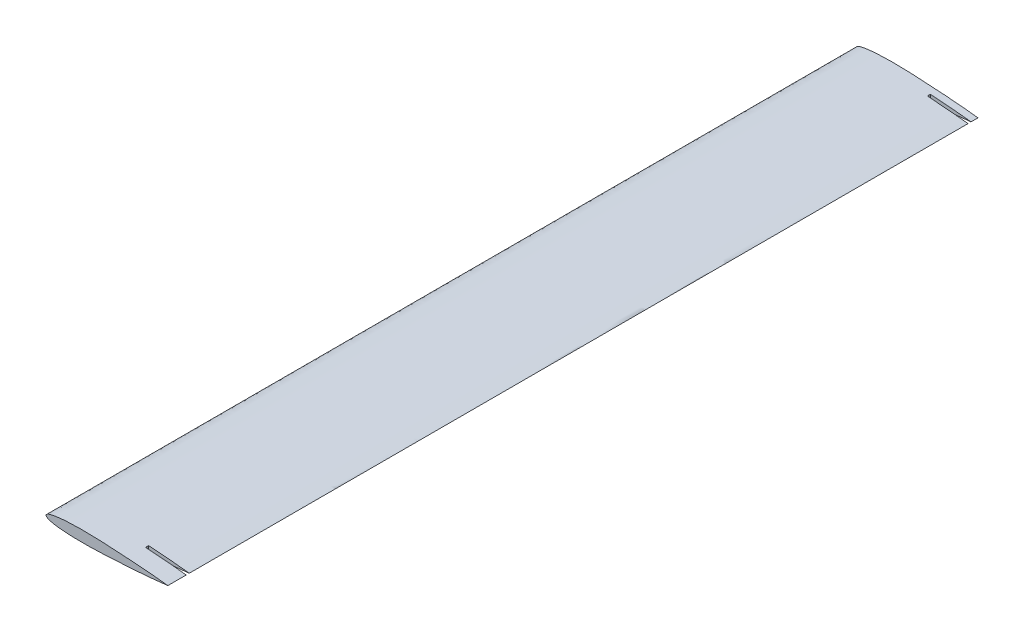
SolidWorks part; units mm, degrees
ref_plane "Front Plane" through (0, 0, 0) normal (0, 0, 1) x (1, 0, 0)
ref_plane "Top Plane" through (0, 0, 0) normal (0, 1, 0) x (1, 0, 0)
ref_plane "Right Plane" through (0, 0, 0) normal (1, 0, 0) x (0, 0, -1)
curve "Curve1"
  spline degree 3 poles (198.173, -0.1902, 0) (200.4592, 0, 0) (198.173, 0.1902, 0) (196.2993, 0.5074, 0) (191.7479, 0.9938, 0) (186.1558, 1.5974, 0) (178.8694, 2.3058, 0) (170.3147, 3.0876, 0) (160.5293, 3.9276, 0) (149.7178, 4.8013, 0) (138.0526, 5.6738, 0) (125.7371, 6.5193, 0) (112.9812, 7.2987, 0) (100.0033, 7.9792, 0) (87.0249, 8.5203, 0) (76.3087, 8.8329, 0) (67.9023, 8.9764, 0) (61.7868, 9.0274, 0) (55.8344, 9.0203, 0) (50.0707, 8.9437, 0) (44.5208, 8.8092, 0) (39.209, 8.606, 0) (34.1575, 8.3417, 0) (29.3873, 8.01, 0) (24.9186, 7.6164, 0) (20.772, 7.1577, 0) (16.9649, 6.6425, 0) (13.512, 6.0841, 0) (10.4279, 5.485, 0) (7.7224, 4.8473, 0) (5.4084, 4.1495, 0) (3.4909, 3.3786, 0) (1.9875, 2.5281, 0) (0.9063, 1.64, 0) (0.2312, 0.826, 0) (-0.0946, 0, 0) (0.2312, -0.826, 0) (0.9063, -1.64, 0) (1.9875, -2.5281, 0) (3.4909, -3.3786, 0) (5.4084, -4.1495, 0) (7.7224, -4.8473, 0) (10.4279, -5.485, 0) (13.512, -6.0841, 0) (16.9649, -6.6425, 0) (20.772, -7.1577, 0) (24.9186, -7.6164, 0) (29.3873, -8.01, 0) (34.1575, -8.3417, 0) (39.209, -8.606, 0) (44.5208, -8.8092, 0) (50.0707, -8.9437, 0) (55.8344, -9.0203, 0) (61.7868, -9.0274, 0) (67.9023, -8.9764, 0) (76.3087, -8.8329, 0) (87.0249, -8.5203, 0) (100.0033, -7.9792, 0) (112.9812, -7.2987, 0) (125.7371, -6.5193, 0) (138.0526, -5.6738, 0) (149.7178, -4.8013, 0) (160.5293, -3.9276, 0) (170.3147, -3.0876, 0) (178.8694, -2.3058, 0) (186.1558, -1.5974, 0) (191.7479, -0.9938, 0) (196.2993, -0.5074, 0) (198.173, -0.1902, 0) (200.4592, 0, 0) (198.173, 0.1902, 0) knots -0.018944 -0.008488 -0.002133 0 0.002133 0.008488 0.018944 0.033319 0.051356 0.072756 0.097141 0.124097 0.153163 0.183834 0.215589 0.247878 0.280151 0.31186 0.327333 0.342463 0.357187 0.371448 0.385183 0.398331 0.410845 0.422673 0.433769 0.44409 0.453589 0.46224 0.47001 0.476871 0.482833 0.487909 0.492155 0.495592 0.498196 0.5 0.501804 0.504408 0.507845 0.512091 0.517167 0.523129 0.52999 0.53776 0.546411 0.55591 0.566231 0.577327 0.589155 0.601669 0.614817 0.628552 0.642813 0.657537 0.672667 0.68814 0.719849 0.752122 0.784411 0.816166 0.846837 0.875903 0.902859 0.927244 0.948644 0.966681 0.981056 0.991512 0.997867 1 1.002133 1.008488 1.018944 periodic
sketch "Sketch1" plane through (0, 0, 0) normal (0, 0, 1) x (1, 0, 0)
  spline S0 degree 3 poles (198.173, -0.1902) (200.4592, 0) (198.173, 0.1902) (196.2993, 0.5074) (191.7479, 0.9938) (186.1558, 1.5974) (178.8694, 2.3058) (170.3147, 3.0876) (160.5293, 3.9276) (149.7178, 4.8013) (138.0526, 5.6738) (125.7371, 6.5193) (112.9812, 7.2987) (100.0033, 7.9792) (87.0249, 8.5203) (76.3087, 8.8329) (67.9023, 8.9764) (61.7868, 9.0274) (55.8344, 9.0203) (50.0707, 8.9437) (44.5208, 8.8092) (39.209, 8.606) (34.1575, 8.3417) (29.3873, 8.01) (24.9186, 7.6164) (20.772, 7.1577) (16.9649, 6.6425) (13.512, 6.0841) (10.4279, 5.485) (7.7224, 4.8473) (5.4084, 4.1495) (3.4909, 3.3786) (1.9875, 2.5281) (0.9063, 1.64) (0.2312, 0.826) (-0.0946, 0) (0.2312, -0.826) (0.9063, -1.64) (1.9875, -2.5281) (3.4909, -3.3786) (5.4084, -4.1495) (7.7224, -4.8473) (10.4279, -5.485) (13.512, -6.0841) (16.9649, -6.6425) (20.772, -7.1577) (24.9186, -7.6164) (29.3873, -8.01) (34.1575, -8.3417) (39.209, -8.606) (44.5208, -8.8092) (50.0707, -8.9437) (55.8344, -9.0203) (61.7868, -9.0274) (67.9023, -8.9764) (76.3087, -8.8329) (87.0249, -8.5203) (100.0033, -7.9792) (112.9812, -7.2987) (125.7371, -6.5193) (138.0526, -5.6738) (149.7178, -4.8013) (160.5293, -3.9276) (170.3147, -3.0876) (178.8694, -2.3058) (186.1558, -1.5974) (191.7479, -0.9938) (196.2993, -0.5074) (198.173, -0.1902) (200.4592, 0) (198.173, 0.1902) knots -0.018944 -0.008488 -0.002133 0 0.002133 0.008488 0.018944 0.033319 0.051356 0.072756 0.097141 0.124097 0.153163 0.183834 0.215589 0.247878 0.280151 0.31186 0.327333 0.342463 0.357187 0.371448 0.385183 0.398331 0.410845 0.422673 0.433769 0.44409 0.453589 0.46224 0.47001 0.476871 0.482833 0.487909 0.492155 0.495592 0.498196 0.5 0.501804 0.504408 0.507845 0.512091 0.517167 0.523129 0.52999 0.53776 0.546411 0.55591 0.566231 0.577327 0.589155 0.601669 0.614817 0.628552 0.642813 0.657537 0.672667 0.68814 0.719849 0.752122 0.784411 0.816166 0.846837 0.875903 0.902859 0.927244 0.948644 0.966681 0.981056 0.991512 0.997867 1 1.002133 1.008488 1.018944 only from (200, 0) to (200, 0) construction
  spline S1 degree 3 poles (198.173, -0.1902) (200.4592, 0) (198.173, 0.1902) (196.2993, 0.5074) (191.7479, 0.9938) (186.1558, 1.5974) (178.8694, 2.3058) (170.3147, 3.0876) (160.5293, 3.9276) (149.7178, 4.8013) (138.0526, 5.6738) (125.7371, 6.5193) (112.9812, 7.2987) (100.0033, 7.9792) (87.0249, 8.5203) (76.3087, 8.8329) (67.9023, 8.9764) (61.7868, 9.0274) (55.8344, 9.0203) (50.0707, 8.9437) (44.5208, 8.8092) (39.209, 8.606) (34.1575, 8.3417) (29.3873, 8.01) (24.9186, 7.6164) (20.772, 7.1577) (16.9649, 6.6425) (13.512, 6.0841) (10.4279, 5.485) (7.7224, 4.8473) (5.4084, 4.1495) (3.4909, 3.3786) (1.9875, 2.5281) (0.9063, 1.64) (0.2312, 0.826) (-0.0946, 0) (0.2312, -0.826) (0.9063, -1.64) (1.9875, -2.5281) (3.4909, -3.3786) (5.4084, -4.1495) (7.7224, -4.8473) (10.4279, -5.485) (13.512, -6.0841) (16.9649, -6.6425) (20.772, -7.1577) (24.9186, -7.6164) (29.3873, -8.01) (34.1575, -8.3417) (39.209, -8.606) (44.5208, -8.8092) (50.0707, -8.9437) (55.8344, -9.0203) (61.7868, -9.0274) (67.9023, -8.9764) (76.3087, -8.8329) (87.0249, -8.5203) (100.0033, -7.9792) (112.9812, -7.2987) (125.7371, -6.5193) (138.0526, -5.6738) (149.7178, -4.8013) (160.5293, -3.9276) (170.3147, -3.0876) (178.8694, -2.3058) (186.1558, -1.5974) (191.7479, -0.9938) (196.2993, -0.5074) (198.173, -0.1902) (200.4592, 0) (198.173, 0.1902) knots -0.018944 -0.008488 -0.002133 0 0.002133 0.008488 0.018944 0.033319 0.051356 0.072756 0.097141 0.124097 0.153163 0.183834 0.215589 0.247878 0.280151 0.31186 0.327333 0.342463 0.357187 0.371448 0.385183 0.398331 0.410845 0.422673 0.433769 0.44409 0.453589 0.46224 0.47001 0.476871 0.482833 0.487909 0.492155 0.495592 0.498196 0.5 0.501804 0.504408 0.507845 0.512091 0.517167 0.523129 0.52999 0.53776 0.546411 0.55591 0.566231 0.577327 0.589155 0.601669 0.614817 0.628552 0.642813 0.657537 0.672667 0.68814 0.719849 0.752122 0.784411 0.816166 0.846837 0.875903 0.902859 0.927244 0.948644 0.966681 0.981056 0.991512 0.997867 1 1.002133 1.008488 1.018944 only from (200, 0) to (200, 0)
extrude "Boss-Extrude1" add sketch "Sketch1" along normal blind 1330
sketch "Sketch2" plane through (0, 0, 1330) normal (0, 0, 1) x (1, 0, 0)
  line L0 (0, 0) -> (200, 0) construction
  spline S0 degree 3 poles (198.173, -0.1902) (200.4592, 0) (198.173, 0.1902) (196.2993, 0.5074) (191.7479, 0.9938) (186.1558, 1.5974) (178.8694, 2.3058) (170.3147, 3.0876) (160.5293, 3.9276) (149.7178, 4.8013) (138.0526, 5.6738) (125.7371, 6.5193) (112.9812, 7.2987) (100.0033, 7.9792) (87.0249, 8.5203) (76.3087, 8.8329) (67.9023, 8.9764) (61.7868, 9.0274) (55.8344, 9.0203) (50.0707, 8.9437) (44.5208, 8.8092) (39.209, 8.606) (34.1575, 8.3417) (29.3873, 8.01) (24.9186, 7.6164) (20.772, 7.1577) (16.9649, 6.6425) (13.512, 6.0841) (10.4279, 5.485) (7.7224, 4.8473) (5.4084, 4.1495) (3.4909, 3.3786) (1.9875, 2.5281) (0.9063, 1.64) (0.2312, 0.826) (-0.0946, 0) (0.2312, -0.826) (0.9063, -1.64) (1.9875, -2.5281) (3.4909, -3.3786) (5.4084, -4.1495) (7.7224, -4.8473) (10.4279, -5.485) (13.512, -6.0841) (16.9649, -6.6425) (20.772, -7.1577) (24.9186, -7.6164) (29.3873, -8.01) (34.1575, -8.3417) (39.209, -8.606) (44.5208, -8.8092) (50.0707, -8.9437) (55.8344, -9.0203) (61.7868, -9.0274) (67.9023, -8.9764) (76.3087, -8.8329) (87.0249, -8.5203) (100.0033, -7.9792) (112.9812, -7.2987) (125.7371, -6.5193) (138.0526, -5.6738) (149.7178, -4.8013) (160.5293, -3.9276) (170.3147, -3.0876) (178.8694, -2.3058) (186.1558, -1.5974) (191.7479, -0.9938) (196.2993, -0.5074) (198.173, -0.1902) (200.4592, 0) (198.173, 0.1902) knots -0.018944 -0.008488 -0.002133 0 0.002133 0.008488 0.018944 0.033319 0.051356 0.072756 0.097141 0.124097 0.153163 0.183834 0.215589 0.247878 0.280151 0.31186 0.327333 0.342463 0.357187 0.371448 0.385183 0.398331 0.410845 0.422673 0.433769 0.44409 0.453589 0.46224 0.47001 0.476871 0.482833 0.487909 0.492155 0.495592 0.498196 0.5 0.501804 0.504408 0.507845 0.512091 0.517167 0.523129 0.52999 0.53776 0.546411 0.55591 0.566231 0.577327 0.589155 0.601669 0.614817 0.628552 0.642813 0.657537 0.672667 0.68814 0.719849 0.752122 0.784411 0.816166 0.846837 0.875903 0.902859 0.927244 0.948644 0.966681 0.981056 0.991512 0.997867 1 1.002133 1.008488 1.018944 only from (200, 0) to (200, 0) construction
sketch "Sketch3" plane through (0, 0, 0) normal (0, 1, 0) x (1, 0, 0)
  line L1 (133.3888, -16.4494) -> (211.7825, -16.4494)
  line L2 (133.3888, -16.4494) -> (133.3888, -11.4494)
  line L3 (133.3888, -11.4494) -> (211.7825, -11.4494)
  line L4 (211.7825, -16.4494) -> (211.7825, -11.4494)
  line L5 (133.3888, -1294.8375) -> (330.7274, -1294.8375)
  line L6 (133.3888, -1294.8375) -> (133.3888, -1299.8375)
  line L7 (133.3888, -1299.8375) -> (330.7274, -1299.8375)
  line L8 (330.7274, -1294.8375) -> (330.7274, -1299.8375)
  dimension "D1" = 5
  dimension "D2" = 5
extrude "Cut-Extrude1" cut sketch "Sketch3" against normal blind 195 and the other way blind 236
